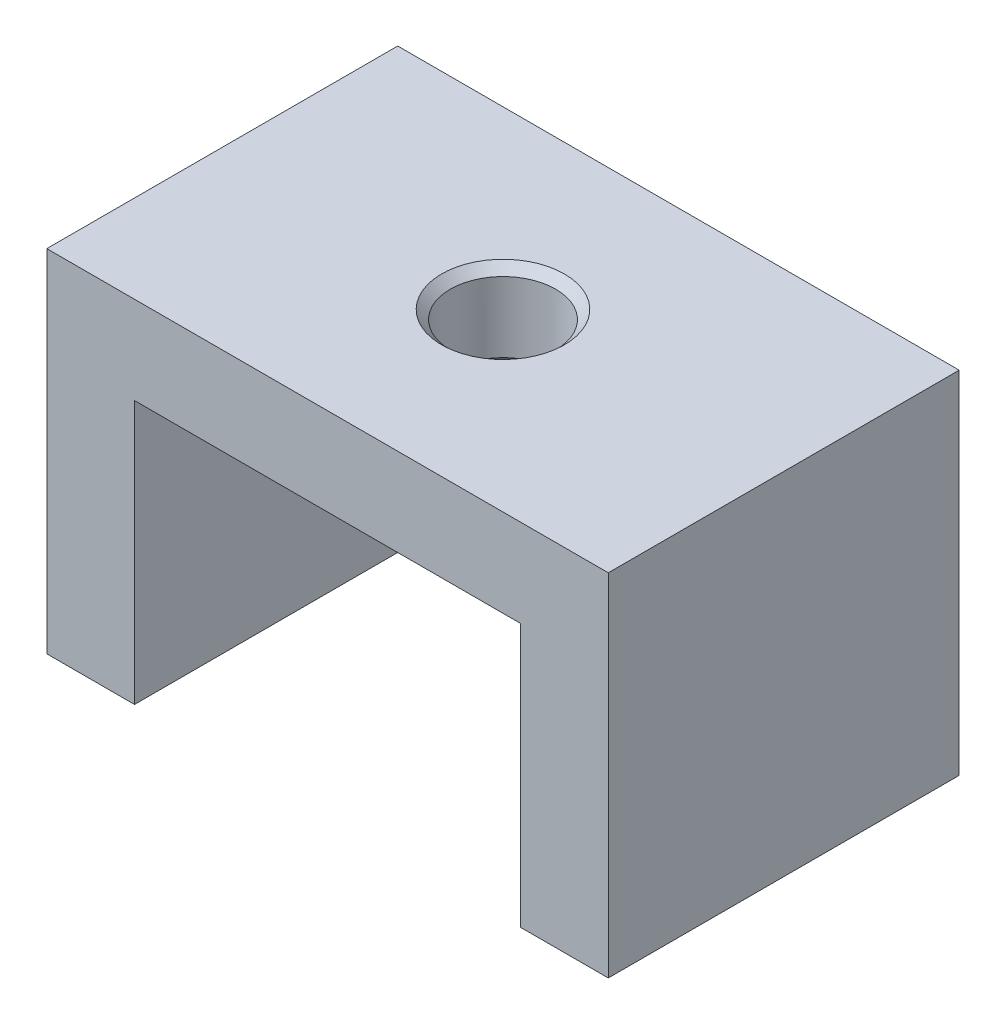
SolidWorks part; units mm, degrees
material "2014-O"
ref_plane "Plan de face" through (0, 0, 0) normal (0, 0, 1) x (1, 0, 0)
ref_plane "Plan de dessus" through (0, 0, 0) normal (0, 1, 0) x (1, 0, 0)
ref_plane "Plan de droite" through (0, 0, 0) normal (1, 0, 0) x (0, 0, -1)
sketch "Esquisse1" plane through (0, 0, 0) normal (0, 0, 1) x (1, 0, 0)
  line L0 (-16, 20) -> (16, 20)
  line L1 (16, 20) -> (16, 0)
  line L2 (16, 0) -> (11, 0)
  line L3 (11, 0) -> (11, 15)
  line L4 (11, 15) -> (-11, 15)
  line L5 (-16, 20) -> (-16, 0)
  line L6 (-16, 0) -> (-11, 0)
  line L7 (-11, 0) -> (-11, 15)
  point P2 (0, 15)
  dimension "D1" = 22
  dimension "D2" = 5
  dimension "D3" = 15
  dimension "D4" = 5
  dimension "D5" = 20
extrude "Boss.-Extru.1" add sketch "Esquisse1" along normal mid plane 20
sketch "Esquisse2" plane through (0, 20, 0) normal (0, 1, 0) x (1, 0, 0)
  circle A0 centre (0, 0) radius 3
  dimension "D1" = 6
extrude "Enlèv. mat.-Extru.1" cut sketch "Esquisse2" against normal through all
chamfer "Chanfrein1" distance 0.5 angle 45 2 edges at (0, 15, 3) (0, 20, 3)
hole_wizard "Trou taraudé M41" positions "Esquisse4" profile "Esquisse3" tap size "M4" standard "ISO"
sketch "Esquisse4" plane through (0, 0, 0) normal (0, -1, 0) x (1, 0, 0)
  line L0 (-16, 10) -> (-16, -10) construction
  line L1 (16, 10) -> (16, -10) construction
  line L2 (11, -10) -> (16, -10) construction
  line L3 (-16, -10) -> (-11, -10) construction
  point P0 (13.5, 5)
  point P1 (-13.5, -5)
  point P14 (-13.5, 5)
  point P16 (13.5, -5)
  dimension "D1" = 2.5
  dimension "D2" = 2.5
  dimension "D3" = 15
  dimension "D4" = 5
sketch "Esquisse3" plane through (13.5, 0, 5) normal (1, 0, 0) x (0, 0, -1)
  line L0 (0, 0) -> (0, 11.0914)
  line L1 (0, 11.0914) -> (1.65, 10.1)
  line L2 (1.65, 10.1) -> (1.65, 0)
  line L5 (1.65, 0) -> (0, 0)
  line L10 (0, 11.0914) -> (-1.65, 10.1) construction
  line L11 (0, -6.35) -> (0, 107.95) construction
  dimension "Diamètre du trou pour taraudage" = 3.3
  dimension "Profondeur du trou pour taraudage" = 10.1
  dimension "Angle de pointe" = 118
cosmetic thread "Filetage de perçage3" parameters "D1"=8, "D2"=4
cosmetic thread "Filetage de perçage4" parameters "D1"=8, "D2"=4
cosmetic thread "Filetage de perçage5" parameters "D1"=8, "D2"=4
cosmetic thread "Filetage de perçage6" parameters "D1"=8, "D2"=4
